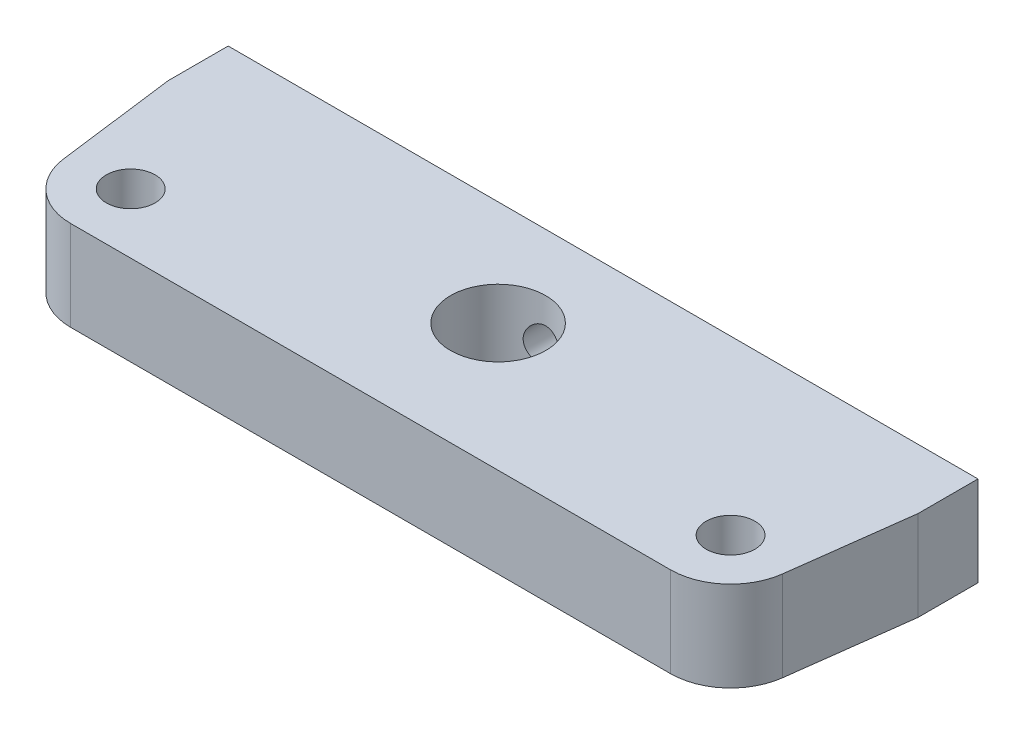
SolidWorks part; units mm, degrees
material "6061-T4 (SS)"
ref_plane "Front Plane" through (0, 0, 0) normal (0, 0, 1) x (1, 0, 0)
ref_plane "Top Plane" through (0, 0, 0) normal (0, 1, 0) x (1, 0, 0)
ref_plane "Right Plane" through (0, 0, 0) normal (1, 0, 0) x (0, 0, -1)
sketch "Sketch1" plane through (0, 0, 0) normal (0, 1, 0) x (1, 0, 0)
  line L0 (-40, 35) -> (40, 35) construction
  line L1 (0, 35) -> (0, 0) construction
  line L2 (-40, 57) -> (40, 57)
  line L4 (38.0933, -18.7323) -> (59.7421, 25.2918)
  line L5 (0, 35) -> (0, 57) construction
  line L6 (0, 0) -> (-47.2553, 0)
  line L7 (-41.2553, -10) -> (-47.2553, -10)
  line L8 (-47.2553, -10) -> (-47.2553, 0)
  line L11 (-47.2553, 3) -> (-32.311, 3)
  line L12 (-47.2553, 3) -> (-59.1799, 24.2237)
  arc A0 (-32.45, 0) -> (-32.311, 3) centre (0, 0) ccw
  arc A1 (-41.2553, -10) -> (38.0933, -18.7323) centre (0, 0) ccw
  circle A2 centre (40, 35) radius 14
  circle A3 centre (-40, 35) radius 14
  arc A6 (-40, 57) -> (-59.1799, 24.2237) centre (-40, 35) ccw
  circle A7 centre (0, 44) radius 5
  arc A8 (59.7421, 25.2918) -> (40, 57) centre (40, 35) ccw
  dimension "D1" = 64.9
  dimension "D2" = 10
  dimension "D4" = 28
  dimension "D6" = 22
  dimension "D7" = 8
  dimension "D8" = 10
  dimension "D9" = 13
  dimension "D3" = 80
  dimension "D5" = 35
  dimension "D10" = 10
  dimension "D11" = 6
  dimension "D12" = 3
extrude "Boss-Extrude1" add sketch "Sketch1" along normal blind 38 contours L4 A8 L2 A6 L12 L11 A0 L6 L8 L7 A1 A2 A3 A7
sketch "Sketch2" plane through (0, 38, 0) normal (0, 1, 0) x (1, 0, 0)
  line L0 (0, 0) -> (0, -38.8647) construction
  line L1 (-40, 57) -> (40, 57) construction
  line L2 (-40, 27) -> (40, 27)
  line L3 (-50, 58) -> (-50, 50)
  line L4 (50, 58) -> (50, 50)
  line L7 (-50, 50) -> (-47.9343, 33.9771)
  line L8 (-50, 58) -> (50, 58)
  line L9 (50, 50) -> (47.9343, 33.9771)
  circle A6 centre (0, 44) radius 6.35
  circle A7 centre (-40, 35) radius 3.25
  circle A8 centre (40, 35) radius 3.25
  circle A10 centre (-40, 35) radius 14 construction
  circle A11 centre (40, 35) radius 14 construction
  arc A18 (-47.9343, 33.9771) -> (-40, 27) centre (-40, 35) ccw
  arc A19 (40, 27) -> (47.9343, 33.9771) centre (40, 35) ccw
  point P22 (0, 58)
  dimension "D2" = 8
  dimension "D3" = 8
  dimension "D4" = 12.7
  dimension "D6" = 6.5
  dimension "D1" = 100
  dimension "D5" = 1
extrude "Boss-Extrude2" add sketch "Sketch2" along normal blind 12 separate body contours A19 L9 L8 L7 A18 L2 | A6
delete or keep bodies "Body-Delete/Keep 1" type delete bodies bodies 101
sketch "Sketch3" plane through (0, 0, -58) normal (0, 0, -1) x (-1, 0, 0)
  line L0 (0, 50) -> (0, 38) construction
  line L1 (-50, 50) -> (50, 50) construction
  line L2 (-50, 38) -> (50, 38) construction
  line L3 (-40, 44) -> (40, 44) construction
  circle A0 centre (0, 44) radius 2.5
  circle A1 centre (40, 44) radius 2.5
  circle A2 centre (-40, 44) radius 2.5
  point P11 (0, 44)
  dimension "D1" = 5
  dimension "D2" = 80
extrude "Cut-Extrude6" cut sketch "Sketch3" against normal blind 10
